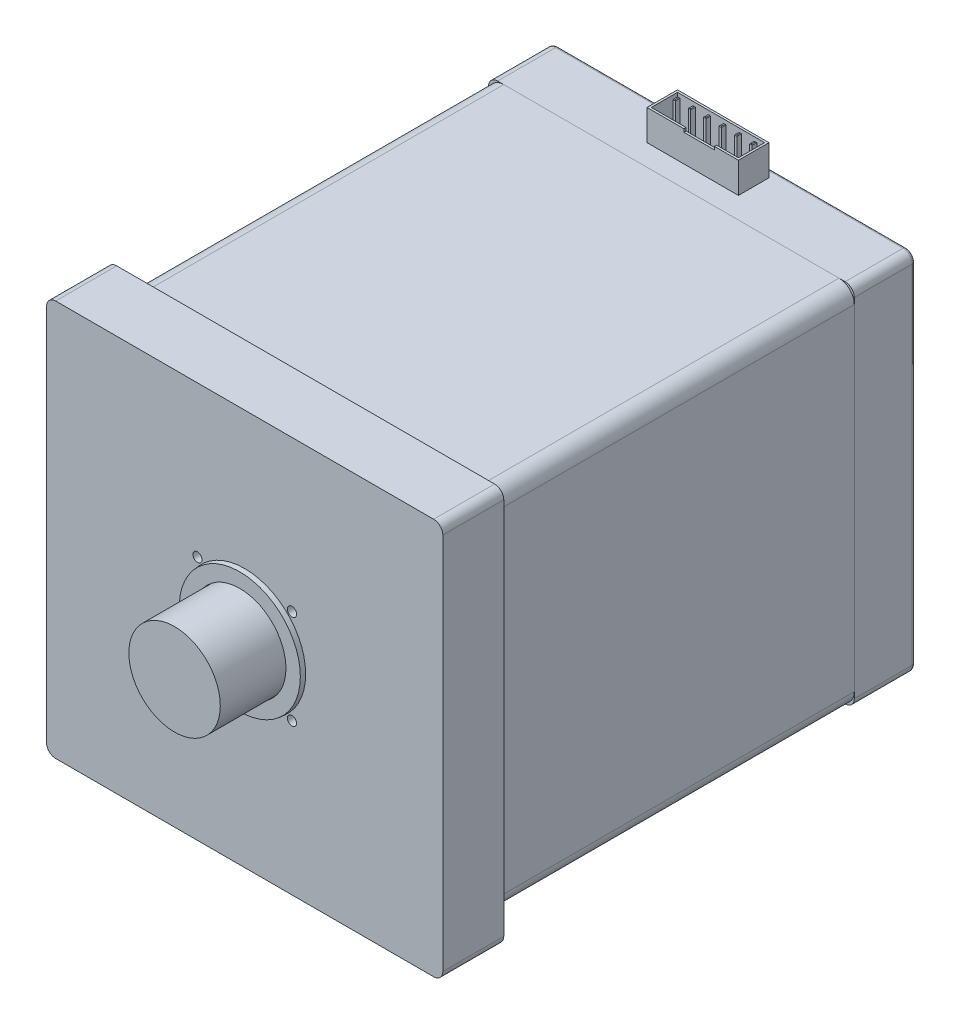
SolidWorks part; units mm, degrees
material "氧化铝"
ref_plane "前视基准面" through (0, 0, 0) normal (0, 0, 1) x (1, 0, 0)
ref_plane "上视基准面" through (0, 0, 0) normal (0, 1, 0) x (1, 0, 0)
ref_plane "右视基准面" through (0, 0, 0) normal (1, 0, 0) x (0, 0, -1)
sketch "草图1" plane through (0, 0, 0) normal (0, 0, 1) x (1, 0, 0)
  line L0 (0, 65) -> (0, -65) construction
  line L1 (-62, 65) -> (62, 65)
  line L2 (-65, 62) -> (-65, -62)
  line L3 (-62, -65) -> (62, -65)
  line L4 (65, 62) -> (65, -62)
  line L5 (-65, 65) -> (65, -65) construction
  line L6 (-65, -65) -> (65, 65) construction
  line L7 (-15.5, 15.5) -> (15.5, 15.5) construction
  line L8 (-15.5, 15.5) -> (-15.5, -15.5) construction
  line L9 (-15.5, -15.5) -> (15.5, -15.5) construction
  line L10 (15.5, 15.5) -> (15.5, -15.5) construction
  line L11 (-15.5, 15.5) -> (15.5, -15.5) construction
  line L12 (-15.5, -15.5) -> (15.5, 15.5) construction
  line L13 (-65, 0) -> (65, 0) construction
  circle A0 centre (-15.5, 15.5) radius 1.5
  circle A1 centre (15.5, 15.5) radius 1.5
  circle A2 centre (15.5, -15.5) radius 1.5
  circle A3 centre (-15.5, -15.5) radius 1.5
  arc A4 (-62, -65) -> (-65, -62) centre (-62, -62) cw
  arc A5 (62, -65) -> (65, -62) centre (62, -62) ccw
  arc A6 (65, 62) -> (62, 65) centre (62, 62) ccw
  arc A7 (-65, 62) -> (-62, 65) centre (-62, 62) cw
  point P0 (0, 0)
  point P6 (0, 0)
  dimension "D4" = 3
  dimension "D5" = 3
  dimension "D1" = 130
  dimension "D2" = 130
  dimension "D3" = 31
extrude "凸台-拉伸1" add sketch "草图1" along normal blind 20
sketch "草图4" plane through (0, 0, 20) normal (0, 0, 1) x (1, 0, 0)
  circle A0 centre (0, 0) radius 15
  dimension "D1" = 30
extrude "凸台-拉伸2" add sketch "草图4" along normal blind 23
sketch "草图9" plane through (0, 0, 0) normal (0, 0, -1) x (-1, 0, 0)
  line L1 (-60, 60) -> (60, 60)
  line L2 (-60, 60) -> (-60, -60)
  line L3 (-60, -60) -> (60, -60)
  line L4 (60, 60) -> (60, -60)
  line L5 (-60, 60) -> (60, -60) construction
  line L6 (-60, -60) -> (60, 60) construction
  point P0 (0, 0)
  dimension "D1" = 120
  dimension "D2" = 120
extrude "凸台-拉伸7" add sketch "草图9" along normal blind 120 separate body
sketch "草图10" plane through (0, 0, -120) normal (0, 0, -1) x (-1, 0, 0)
  line L1 (-60, 60) -> (60, 60)
  line L2 (-60, 60) -> (-60, -60)
  line L3 (-60, -60) -> (60, -60)
  line L4 (60, 60) -> (60, -60)
extrude "凸台-拉伸8" add sketch "草图10" along normal blind 20 separate body
fillet "圆角1" radius 3 4 edges at (60, -60, -130) (-60, -60, -130) (-60, 60, -130) (60, 60, -130)
fillet "圆角2" radius 5 4 edges at (-60, -60, -60) (-60, 60, -60) (60, 60, -60) (60, -60, -60)
sketch "草图12" plane through (0, 0, 20) normal (0, 0, 1) x (1, 0, 0)
  circle A0 centre (-15.5, 15.5) radius 1.5
  circle A1 centre (15.5185, 15.5) radius 1.5185
  circle A2 centre (-15.5, -15.5) radius 1.5
  circle A3 centre (15.5, -15.5) radius 1.5
extrude "切除-拉伸1" cut sketch "草图12" against normal through all
sketch "草图13" plane through (0, 0, -140) normal (0, 0, -1) x (-1, 0, 0)
  circle A0 centre (0, 0) radius 2.5
extrude "凸台-拉伸9" [suppressed] add sketch "草图13" along normal blind 12
sketch "草图14" plane through (0, 60, 0) normal (0, 1, 0) x (1, 0, 0)
  line L0 (-57, 140) -> (57, 140) construction
  line L1 (-15, 137) -> (15, 137)
  line L2 (-15, 137) -> (-15, 127)
  line L3 (-15, 127) -> (15, 127)
  line L4 (15, 137) -> (15, 127)
  line L5 (-14.3, 136.3) -> (14.3, 136.3)
  line L6 (14.3, 136.3) -> (14.3, 127.7)
  line L7 (-14.3, 127.7) -> (14.3, 127.7)
  line L8 (-14.3, 136.3) -> (-14.3, 127.7)
  line L9 (-8.16, 135.2073) -> (-7.36, 135.2073)
  line L10 (-13.2, 135.2073) -> (-12.4, 135.2073)
  line L11 (-13.2, 135.2073) -> (-13.2, 133.7073)
  line L12 (-13.2, 133.7073) -> (-12.4, 133.7073)
  line L13 (-12.4, 135.2073) -> (-12.4, 133.7073)
  line L14 (-13.2, 135.2073) -> (-12.4, 133.7073) construction
  line L15 (-13.2, 133.7073) -> (-12.4, 135.2073) construction
  line L16 (-8.16, 135.2073) -> (-8.16, 133.7073)
  line L17 (-8.16, 133.7073) -> (-7.36, 133.7073)
  line L18 (-7.36, 135.2073) -> (-7.36, 133.7073)
  line L19 (-8.16, 135.2073) -> (-7.36, 133.7073) construction
  line L20 (-8.16, 133.7073) -> (-7.36, 135.2073) construction
  line L21 (-3.12, 135.2073) -> (-2.32, 135.2073)
  line L22 (-3.12, 135.2073) -> (-3.12, 133.7073)
  line L23 (-3.12, 133.7073) -> (-2.32, 133.7073)
  line L24 (-2.32, 135.2073) -> (-2.32, 133.7073)
  line L25 (-3.12, 135.2073) -> (-2.32, 133.7073) construction
  line L26 (-3.12, 133.7073) -> (-2.32, 135.2073) construction
  line L27 (1.92, 135.2073) -> (2.72, 135.2073)
  line L28 (1.92, 135.2073) -> (1.92, 133.7073)
  line L29 (1.92, 133.7073) -> (2.72, 133.7073)
  line L30 (2.72, 135.2073) -> (2.72, 133.7073)
  line L31 (1.92, 135.2073) -> (2.72, 133.7073) construction
  line L32 (1.92, 133.7073) -> (2.72, 135.2073) construction
  line L33 (6.96, 135.2073) -> (7.76, 135.2073)
  line L34 (6.96, 135.2073) -> (6.96, 133.7073)
  line L35 (6.96, 133.7073) -> (7.76, 133.7073)
  line L36 (7.76, 135.2073) -> (7.76, 133.7073)
  line L37 (6.96, 135.2073) -> (7.76, 133.7073) construction
  line L38 (6.96, 133.7073) -> (7.76, 135.2073) construction
  line L39 (12, 135.2073) -> (12.8, 135.2073)
  line L40 (12, 135.2073) -> (12, 133.7073)
  line L41 (12, 133.7073) -> (12.8, 133.7073)
  line L42 (12.8, 135.2073) -> (12.8, 133.7073)
  line L43 (12, 135.2073) -> (12.8, 133.7073) construction
  line L44 (12, 133.7073) -> (12.8, 135.2073) construction
  line L45 (0, 140) -> (0, 137) construction
  point P11 (-12.8, 134.4573)
  point P18 (-7.76, 134.4573)
  point P23 (-2.72, 134.4573)
  point P28 (2.32, 134.4573)
  point P33 (7.36, 134.4573)
  point P38 (12.4, 134.4573)
  dimension "D1" = 30
  dimension "D2" = 10
  dimension "D3" = 3
  dimension "D4" = 0.7
  dimension "D5" = 1.5
  dimension "D6" = 0.8
  dimension "D8" = 1.5
  dimension "D9" = 1.5
  dimension "D7" = 6
extrude "凸台-拉伸10" add sketch "草图14" along normal blind 10 contours L4 L1 L2 L3 L8 L5 L6 L7 | L13 L10 L11 L12 | L24 L21 L22 L23 | L42 L39 L40 L41 | L36 L33 L34 L35 | L9 L18 L17 L16 | L27 L30 L29 L28
chamfer "倒角1" distance 0.2 angle 45 24 edges at (12.4, 70, -133.7073) (12, 70, -134.4573) (12.4, 70, -135.2073) (12.8, 70, -134.4573) (7.36, 70, -133.7073) (6.96, 70, -134.4573) (7.36, 70, -135.2073) (7.76, 70, -134.4573) (2.32, 70, -135.2073) (2.72, 70, -134.4573) (2.32, 70, -133.7073) (1.92, 70, -134.4573) (-2.72, 70, -133.7073) (-3.12, 70, -134.4573) (-2.72, 70, -135.2073) (-2.32, 70, -134.4573) (-7.76, 70, -135.2073) (-7.36, 70, -134.4573) (-7.76, 70, -133.7073) (-8.16, 70, -134.4573) (-12.8, 70, -133.7073) (-13.2, 70, -134.4573) (-12.8, 70, -135.2073) (-12.4, 70, -134.4573)
sketch "草图15" plane through (0, 0, -127) normal (0, 0, 1) x (1, 0, 0)
  line L0 (2.12, 70) -> (2.12, 22.2151) construction
  line L1 (-2.88, 70) -> (-2.88, 69)
  line L2 (-15, 70) -> (15, 70) construction
  line L3 (-2.88, 69) -> (7.12, 69)
  line L4 (7.12, 70) -> (7.12, 69)
  line L5 (-2.88, 70) -> (7.12, 70)
  point P9 (2.12, 69)
  dimension "D1" = 5
  dimension "D2" = 1
extrude "切除-拉伸2" cut sketch "草图15" against normal up to next (0.7 mm away)
fillet "圆角3" radius 1 8 edges at (59.1213, 59.1213, -140) (-59.1213, 59.1213, -140) (-60, 0, -140) (-59.1213, -59.1213, -140) (0, -60, -140) (59.1213, -59.1213, -140) (60, 0, -140) (0, 60, -140)
sketch "草图16" plane through (0, 0, 20) normal (0, 0, 1) x (1, 0, 0)
  circle A0 centre (0, 0) radius 20
  circle A1 centre (0, 0) radius 15 construction
  circle A2 centre (0, 0) radius 15
  dimension "D1" = 40
extrude "凸台-拉伸11" add sketch "草图16" along normal blind 1.6 draft 5
sketch "草图17" plane through (0, 0, -140) normal (0, 0, -1) x (-1, 0, 0)
  circle A0 centre (0, 0) radius 2.5
  dimension "D1" = 5
extrude "凸台-拉伸12" [suppressed] add sketch "草图17" along normal blind 15
